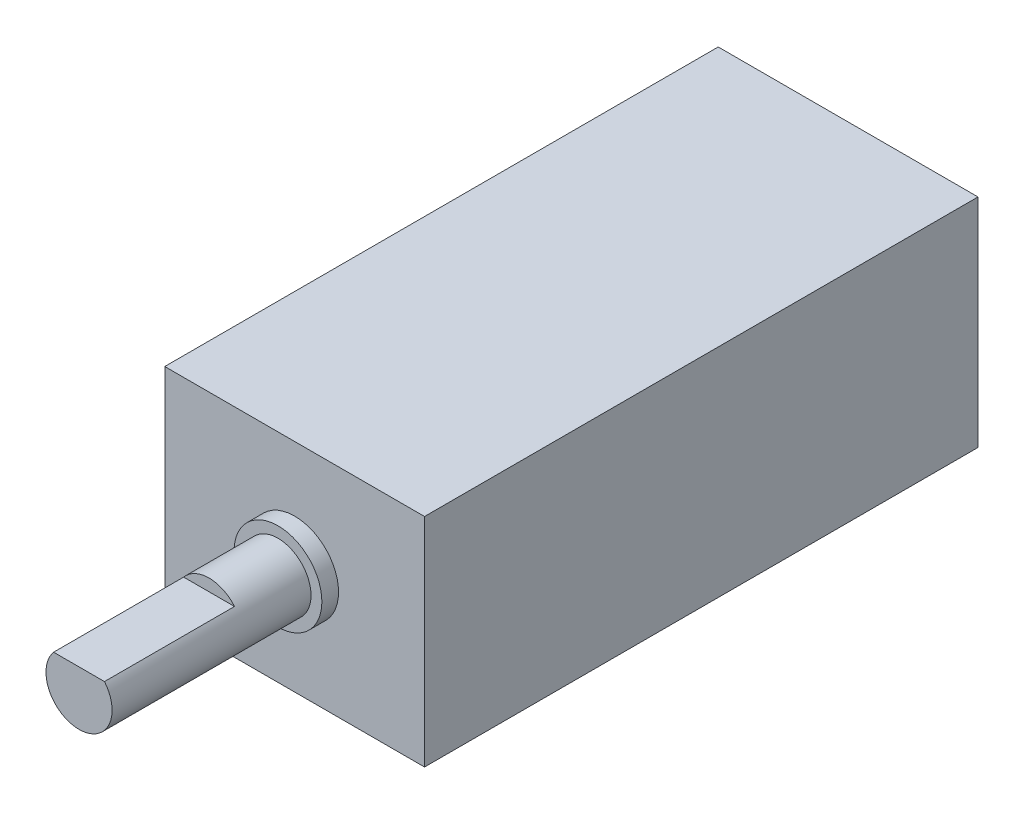
SolidWorks part; units mm, degrees
ref_plane "Front Plane" through (0, 0, 0) normal (0, 0, 1) x (1, 0, 0)
ref_plane "Top Plane" through (0, 0, 0) normal (0, 1, 0) x (1, 0, 0)
ref_plane "Right Plane" through (0, 0, 0) normal (1, 0, 0) x (0, 0, -1)
sketch "Sketch1" plane through (0, 0, 0) normal (0, 0, 1) x (1, 0, 0)
  line L1 (-5.9372, -4.9594) -> (5.9373, -4.9594)
  line L2 (-5.9372, -4.9594) -> (-5.9372, 4.9594)
  line L3 (-5.9372, 4.9594) -> (5.9373, 4.9594)
  line L4 (5.9373, -4.9594) -> (5.9373, 4.9594)
  line L5 (-5.9372, -4.9594) -> (5.9373, 4.9594) construction
  line L6 (-5.9372, 4.9594) -> (5.9373, -4.9594) construction
  point P0 (0, 0)
  dimension "D1" = 9.9187
  dimension "D2" = 11.8745
extrude "Boss-Extrude1" add sketch "Sketch1" against normal blind 25.2984
sketch "Sketch2" plane through (0, 0, 0) normal (0, 0, 1) x (1, 0, 0)
  circle A0 centre (0, 0) radius 2.0066
  dimension "D1" = 4.0132
extrude "Boss-Extrude2" add sketch "Sketch2" along normal blind 0.762
sketch "Sketch3" plane through (0, 0, 0.762) normal (0, 0, 1) x (1, 0, 0)
  circle A0 centre (0, 0) radius 1.5113
  dimension "D1" = 3.0226
extrude "Boss-Extrude3" add sketch "Sketch3" along normal blind 9.0932
sketch "Sketch4" plane through (0, 0, 9.8552) normal (0, 0, 1) x (1, 0, 0)
  line L0 (-1.6676, 0.9652) -> (2.042, 0.9652)
  line L1 (0, 0) -> (0, 2.4788) construction
  line L2 (-1.7815, 1.5113) -> (2.042, 1.5113) construction
  circle A1 centre (0, 0) radius 1.5113
  circle A2 centre (0, 0) radius 1.5113
  circle M4 centre (0, 0) radius 1.5113
  dimension "D2" = 0.5461
  dimension "D1" = 0
extrude "Cut-Extrude1" cut sketch "Sketch4" against normal blind 5.9436 contours L0 M4
